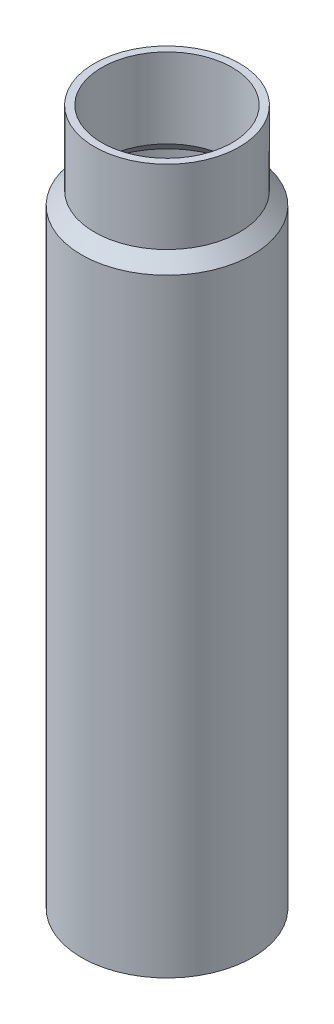
SolidWorks part; units mm, degrees
ref_plane "Front Plane" through (0, 0, 0) normal (0, 0, 1) x (1, 0, 0)
ref_plane "Top Plane" through (0, 0, 0) normal (0, 1, 0) x (1, 0, 0)
ref_plane "Right Plane" through (0, 0, 0) normal (1, 0, 0) x (0, 0, -1)
sketch "Sketch3" plane through (0, 0, 0) normal (0, 0, 1) x (1, 0, 0)
  line L0 (0, 0) -> (37.465, 0)
  line L1 (37.465, 0) -> (37.465, 266.7)
  line L2 (37.465, 266.7) -> (31.75, 272.415)
  line L3 (31.75, 272.415) -> (31.75, 304.8)
  line L4 (31.75, 304.8) -> (28.575, 304.8)
  line L5 (0, 3.175) -> (0, 0)
  line L6 (0, 3.175) -> (34.925, 3.175)
  line L7 (34.925, 3.175) -> (34.925, 263.525)
  line L8 (34.925, 263.525) -> (28.575, 269.875)
  line L9 (28.575, 269.875) -> (28.575, 304.8)
  line L10 (0, 0) -> (0, 387.2752) construction
  dimension "D1" = 37.465
  dimension "D2" = 34.925
  dimension "D3" = 3.175
  dimension "D4" = 31.75
  dimension "D5" = 3.175
  dimension "D6" = 304.8
  dimension "D7" = 266.7
  dimension "D8" = 2.54
  dimension "D9" = 135
revolve "Revolve1" add sketch "Sketch3" angle 360 about L10
